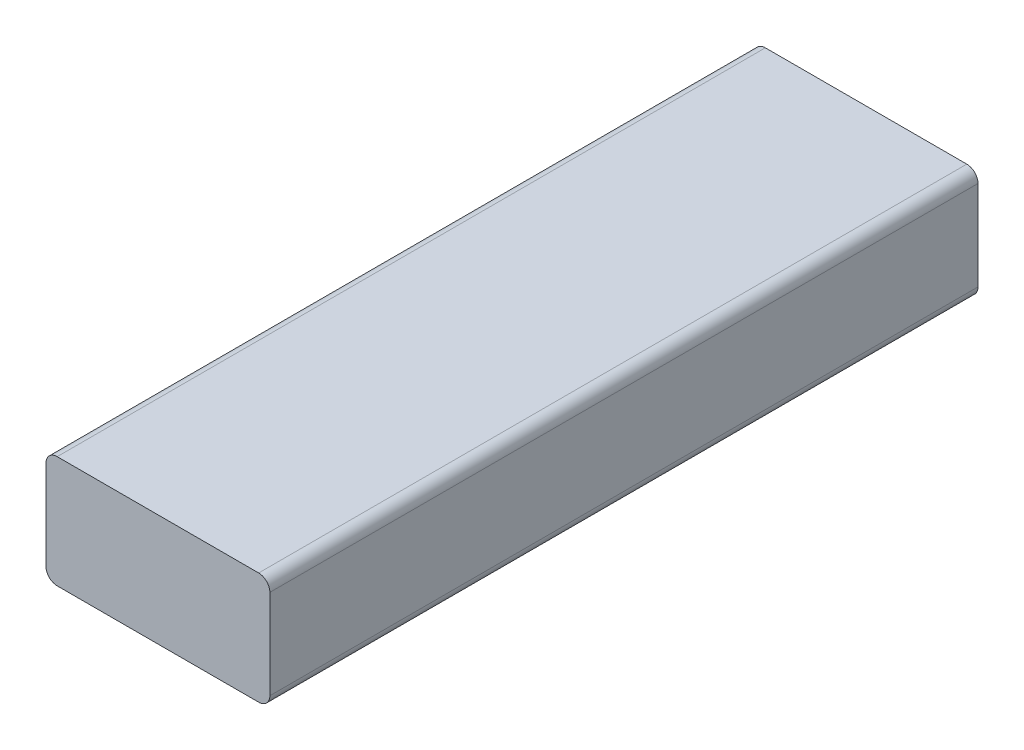
SolidWorks part; units mm, degrees
material "Balsa"
ref_plane "Front Plane" through (0, 0, 0) normal (0, 0, 1) x (1, 0, 0)
ref_plane "Top Plane" through (0, 0, 0) normal (0, 1, 0) x (1, 0, 0)
ref_plane "Right Plane" through (0, 0, 0) normal (1, 0, 0) x (0, 0, -1)
sketch "Sketch1" plane through (0, -12.7, 0) normal (0, -1, 0) x (-1, 0, 0)
  line L0 (-1812.7, 160.7) -> (-2587.3, 160.7) construction
  line L1 (-2587.3, 160.7) -> (-2485.7, 160.7)
  line L2 (-2587.3, 160.7) -> (-2587.3, -160.7)
  line L3 (-2587.3, -160.7) -> (-2485.7, -160.7)
  line L4 (-2485.7, 160.7) -> (-2485.7, -160.7)
  line L5 (-2587.3, -275) -> (-2587.3, 275) construction
  line L6 (-2587.3, -160.7) -> (-1812.7, -160.7) construction
  dimension "D1" = 101.6
extrude "Boss-Extrude1" add sketch "Sketch1" against normal blind 50.8
fillet "Fillet1" radius 5.08 4 edges at (2587.3, -12.7, 0) (2485.7, -12.7, 0) (2587.3, 38.1, 0) (2485.7, 38.1, 0)
